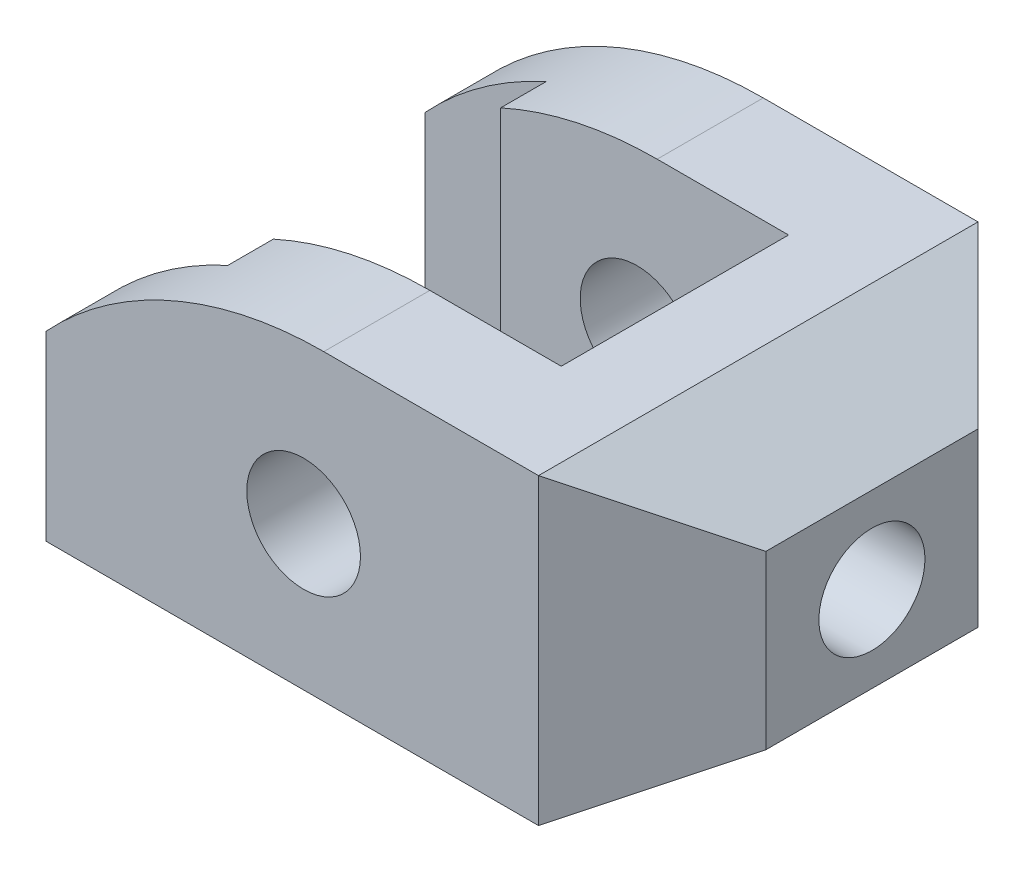
SolidWorks part; units mm, degrees
material "1060 Alloy"
ref_plane "Front Plane" through (0, 0, 0) normal (0, 0, 1) x (1, 0, 0)
ref_plane "Top Plane" through (0, 0, 0) normal (0, 1, 0) x (1, 0, 0)
ref_plane "Right Plane" through (0, 0, 0) normal (1, 0, 0) x (0, 0, -1)
sketch "Sketch1" plane through (0, 0, 0) normal (0, 0, 1) x (1, 0, 0)
  line L0 (-34, -19) -> (31, -19)
  line L1 (-34, -19) -> (-34, 5)
  line L2 (31, -19) -> (31, 21) construction
  line L3 (31, 21) -> (2.6606, 21)
  line L4 (31, 21) -> (46, 12.3397)
  line L5 (31, -19) -> (46, -10.3397)
  line L6 (46, 12.3397) -> (46, -10.3397)
  circle A0 centre (0, 0) radius 7.5
  arc A1 (-34, 5) -> (2.6606, 21) centre (2.6606, -29) cw
  dimension "D1" = 15
  dimension "D4" = 31
  dimension "D7" = 50
  dimension "D2" = 65
  dimension "D3" = 19
  dimension "D5" = 24
  dimension "D6" = 40
  dimension "D8" = 30
  dimension "D9" = 15
  dimension "D10" = 30
  dimension "D11" = 15
extrude "Boss-Extrude1" add sketch "Sketch1" along normal blind 58
sketch "Sketch5" plane through (46, 0, 0) normal (1, 0, 0) x (0, 0, -1)
  line L0 (-58, 1) -> (0, 1) construction
  line L1 (-58, -10.3397) -> (-58, 12.3397) construction
  line L2 (0, -10.3397) -> (0, 12.3397) construction
  circle A0 centre (-29, 1) radius 7
  dimension "D1" = 14
extrude "Cut-Extrude1" cut sketch "Sketch5" against normal through all
sketch "Sketch6" plane through (0, 0, 0) normal (0, 1, 0) x (1, 0, 0)
  line L0 (-34, -14) -> (20, -14)
  line L1 (-34, -23.2554) -> (-34, 0) construction
  line L2 (20, -14) -> (20, -44)
  line L3 (-34, -44) -> (20, -44)
  line L4 (-34, -58) -> (-34, -34.7446) construction
  dimension "D1" = 14
  dimension "D2" = 14
  dimension "D3" = 11
extrude "Cut-Extrude3" cut sketch "Sketch6" against normal through all and the other way through all contours L0 L2 L3
sketch "Sketch7" plane through (0, 0, 0) normal (0, 1, 0) x (1, 0, 0)
  line L0 (-34, -8) -> (-18, -8)
  line L1 (-34, -14) -> (-34, 0) construction
  line L2 (-18, -8) -> (-18, -14)
  line L3 (-34, -14) -> (2.6606, -14) construction
  line L4 (-34, -50) -> (-18, -50)
  line L5 (-34, -58) -> (-34, -44) construction
  line L6 (-18, -50) -> (-18, -44)
  line L7 (2.6606, -44) -> (-34, -44) construction
  line L8 (-18, -44) -> (-34, -44)
  line L9 (-34, -44) -> (-34, -50)
  line L10 (-34, -8) -> (-34, -14)
  line L11 (-34, -14) -> (-18, -14)
  dimension "D1" = 8
  dimension "D2" = 16
  dimension "D3" = 8
  dimension "D4" = 16
extrude "Cut-Extrude5" cut sketch "Sketch7" against normal through all and the other way through all
sketch "Sketch14" plane through (0, 0, 0) normal (0, 1, 0) x (1, 0, 0)
  line L0 (31, 0) -> (46, 0)
  line L1 (46, 0) -> (46, -15)
  line L2 (46, -58) -> (46, 0) construction
  line L3 (46, -15) -> (31, 0)
  line L4 (31, -58) -> (46, -58)
  line L5 (46, -58) -> (46, -43)
  line L6 (46, -43) -> (31, -58)
  dimension "D1" = 45
  dimension "D2" = 45
extrude "Cut-Extrude14" cut sketch "Sketch14" against normal blind 24 and the other way blind 24
equation "\"A\"= 58mm"
equation "\"B\"= 40mm"
equation "\"C\"= 65mm"
